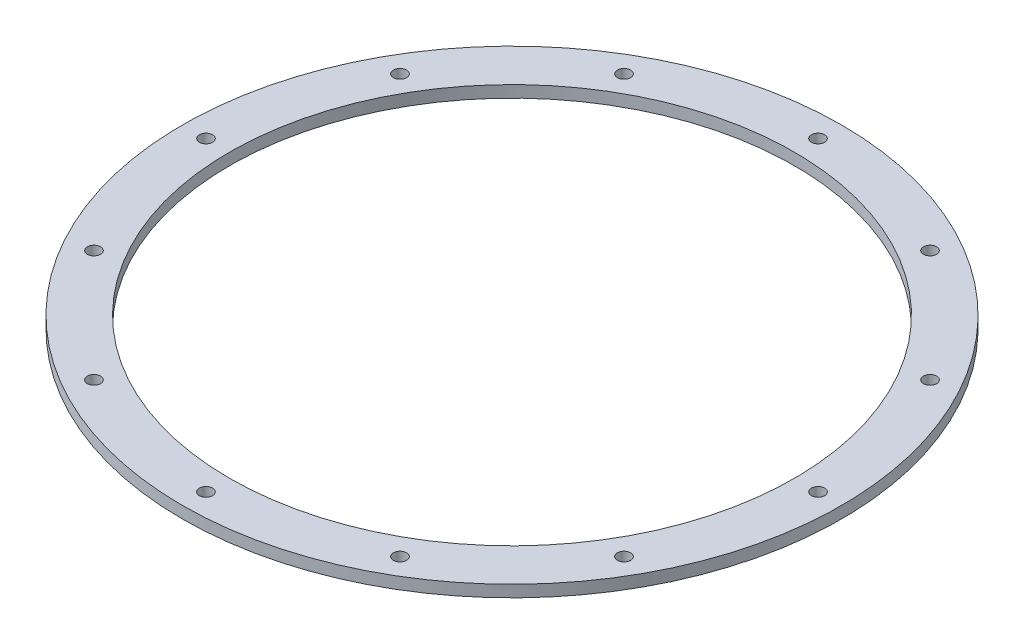
SolidWorks part; units mm, degrees
material "PTFE (general)"
ref_plane "Front Plane" through (0, 0, 0) normal (0, 0, 1) x (1, 0, 0)
ref_plane "Top Plane" through (0, 0, 0) normal (0, 1, 0) x (1, 0, 0)
ref_plane "Right Plane" through (0, 0, 0) normal (1, 0, 0) x (0, 0, -1)
ref_axis "Axis1" through (0, 55, 0) along (0, -1, 0)
sketch "Sketch1" plane through (0, 0, 0) normal (0, 0, 1) x (1, 0, 0)
  line L0 (-38.1, 0) -> (0, 0) construction
  line L1 (-38.1, 0) -> (-44.45, 0)
  line L2 (-38.1, 0) -> (-38.1, 1.5875)
  line L3 (-38.1, 1.5875) -> (-44.45, 1.5875)
  line L4 (-44.45, 0) -> (-44.45, 1.5875)
  line L7 (0, 1.5875) -> (-38.1, 1.5875) construction
  point P12 (-44.45, 0)
  point P18 (-38.1, 1.5875)
revolve "Main" add sketch "Sketch1" angle 360 about axis through (0, 55, 0) along (0, -1, 0)
sketch "Hole Location" plane through (0, 0, 0) normal (0, 1, 0) x (1, 0, 0)
  line L0 (0, 0) -> (-41.275, 0) construction
  circle A0 centre (0, 0) radius 41.275 construction
  dimension "D1" = 82.55
hole_wizard "#50 (0.07) Diameter Hole1" positions "Sketch3" profile "Sketch5" hole size "#50" standard "ANSI Inch" end condition through all
sketch "Sketch3" plane through (0, 0, 0) normal (0, -1, 0) x (-1, 0, 0)
  point P0 (41.275, 0)
sketch "Sketch5" plane through (-41.275, 0, 0) normal (1, 0, 0) x (0, 0, -1)
  line L0 (0, 0) -> (0, 1.5875)
  line L1 (0, 1.5875) -> (0.889, 1.5875)
  line L2 (0.889, 1.5875) -> (0.889, 0)
  line L5 (0.889, 0) -> (0, 0)
  line L11 (0, -6.35) -> (0, 107.95) construction
  dimension "Thru Hole Dia." = 1.778
  dimension "Thru Hole Depth" = 1.5875
pattern_circular "Screw Passthroughs" count 12 over 360 about axis through (0, 0, 0) along (0, 1, 0) of "#50 (0.07) Diameter Hole1"
equation "\"D1@Hole Location\"=\"TANK DIAMETER@Cryo Tank.SLDASM\"+\"GASKET SEAT THICKNESS@Cryo Tank.SLDASM\""
